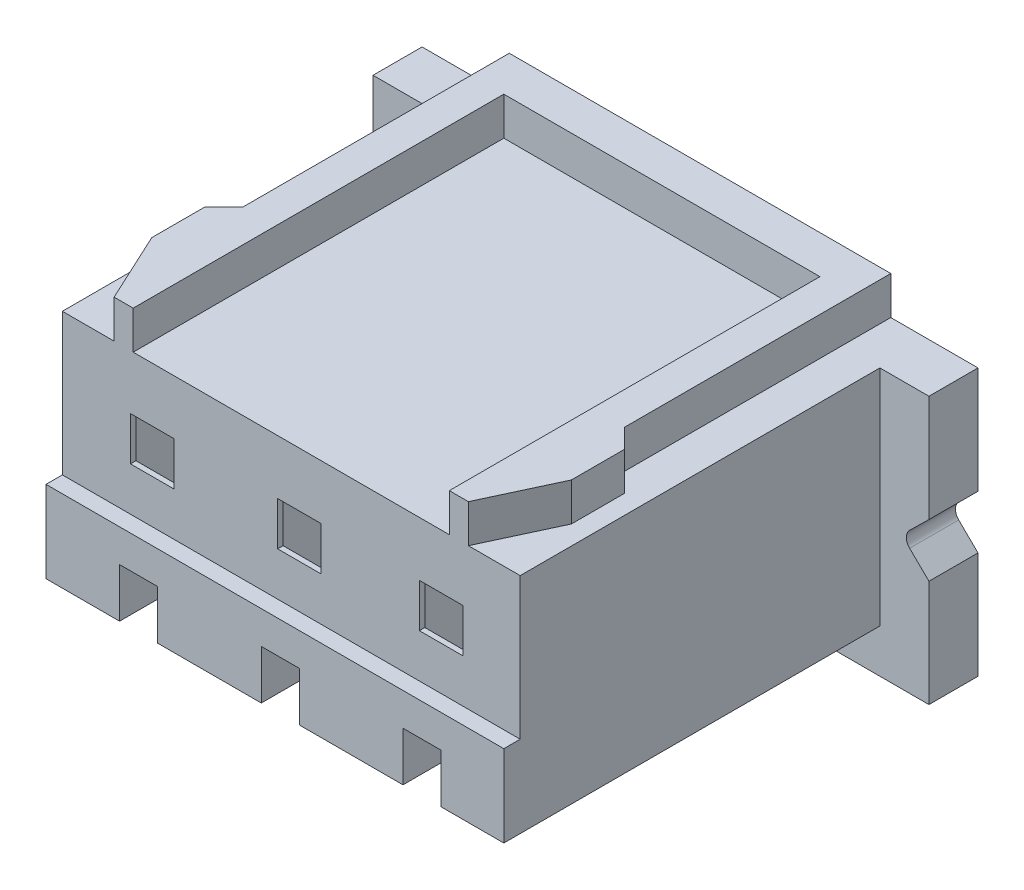
SolidWorks part; units mm, degrees
ref_plane "Plan de face" through (0, 0, 0) normal (0, 0, 1) x (1, 0, 0)
ref_plane "Plan de dessus" through (0, 0, 0) normal (0, 1, 0) x (1, 0, 0)
ref_plane "Plan de droite" through (0, 0, 0) normal (1, 0, 0) x (0, 0, -1)
sketch "Esquisse1" plane through (0, 0, 0) normal (0, 0, 1) x (1, 0, 0)
  line L1 (-5.1, 2.8) -> (5.1, 2.8)
  line L2 (-5.1, 2.8) -> (-5.1, -2.8)
  line L3 (-5.1, -2.8) -> (5.1, -2.8)
  line L4 (5.1, 2.8) -> (5.1, -2.8)
  line L5 (-5.1, 2.8) -> (5.1, -2.8) construction
  line L6 (-5.1, -2.8) -> (5.1, 2.8) construction
  point P0 (0, 0)
  dimension "D1" = 10.2
  dimension "D2" = 5.6
extrude "Boss.-Extru.1" add sketch "Esquisse1" against normal blind 7.8
sketch "Esquisse2" plane through (0, 0, 0) normal (0, 0, 1) x (1, 0, 0)
  line L0 (5.1, -2.8) -> (5.1, 2.8) construction
  line L1 (-5.1, 2.8) -> (5.1, 2.8)
  line L2 (-5.1, 2.8) -> (-5.1, -0.5)
  line L3 (-5.1, -0.5) -> (5.1, -0.5)
  line L4 (5.1, 2.8) -> (5.1, -0.5)
  dimension "D1" = 3.3
extrude "Enlèv. mat.-Extru.1" cut sketch "Esquisse2" against normal blind 0.3
sketch "Esquisse4" plane through (0, 0, 0) normal (0, 0, 1) x (1, 0, 0)
  line L0 (5.1, 2.8) -> (-5.1, 2.8) construction
  line L1 (-5.1, -2.8) -> (5.1, -2.8) construction
  line L2 (5.1, 2.8) -> (-5.1, 2.8)
  line L3 (-5.1, -2.8) -> (5.1, -2.8)
  line L4 (-4.2, 2.8) -> (-4.2, -2)
  line L5 (-4.2, -2) -> (4.2, -2)
  line L6 (4.2, -2) -> (4.2, 2.8)
  line L7 (-5.1, 2.8) -> (-5.1, -0.5) construction
  line L8 (5.1, -0.5) -> (5.1, 2.8) construction
  line L9 (-5.1, -0.5) -> (-5.1, -2.8) construction
  line L10 (5.1, -2.8) -> (5.1, -0.5) construction
  line L11 (-5.1, 2.8) -> (-5.1, -0.5)
  line L12 (-5.1, -0.5) -> (-5.1, -2.8)
  line L13 (5.1, -2.8) -> (5.1, -0.5)
  line L14 (5.1, -0.5) -> (5.1, 2.8)
  line M1 (5.1, -0.5) -> (-5.1, -0.5)
  line M2 (-5.1, -0.5) -> (-5.1, -2.8)
  line M3 (-5.1, -2.8) -> (5.1, -2.8)
  line M4 (5.1, -2.8) -> (5.1, -0.5)
  dimension "D1" = 0.9
  dimension "D2" = 0.9
  dimension "D3" = 0.8
extrude "Enlèv. mat.-Extru.2" cut sketch "Esquisse4" against normal blind 6.9 contours L2 L11 L4 M1 | L6 L5 L4 M1 M2 M3 M4 | L14 L2 L6 M1
sketch "Esquisse5" plane through (0, 2.8, 0) normal (0, 1, 0) x (1, 0, 0)
  line L0 (-3.5, 7.8) -> (-3.5, 2.91)
  line L1 (-3.5, 2.91) -> (-3.85, 2.56)
  line L2 (-3.85, 2.56) -> (-3.85, 1.59)
  line L3 (-3.85, 1.59) -> (-3.25, 0.3)
  line L4 (4.2, 0.3) -> (-4.2, 0.3) construction
  line L5 (-2.9, 0.3) -> (-2.9, 7.1)
  line L6 (-2.9, 7.1) -> (2.9, 7.1)
  line L7 (0, 7.8) -> (0, 0.3) construction
  line L8 (-5.1, 6.9) -> (-4.2, 6.9)
  line L9 (-4.2, 6.9) -> (-4.2, 0.3)
  line L10 (-4.2, 0.3) -> (4.2, 0.3)
  line L11 (4.2, 0.3) -> (4.2, 6.9)
  line L12 (4.2, 6.9) -> (5.1, 6.9)
  line L13 (5.1, 6.9) -> (5.1, 7.8)
  line L14 (5.1, 7.8) -> (-5.1, 7.8)
  line L15 (-5.1, 7.8) -> (-5.1, 6.9)
  line L16 (-5.1, 6.9) -> (-4.2, 6.9)
  line L17 (-4.2, 6.9) -> (-4.2, 0.3)
  line L18 (-4.2, 0.3) -> (4.2, 0.3)
  line L19 (4.2, 0.3) -> (4.2, 6.9)
  line L20 (4.2, 6.9) -> (5.1, 6.9)
  line L21 (5.1, 6.9) -> (5.1, 7.8)
  line L22 (5.1, 7.8) -> (-5.1, 7.8)
  line L23 (-5.1, 7.8) -> (-5.1, 6.9)
  line L24 (5.1, 7.8) -> (5.1, 6.9)
  line L25 (4.2, 6.9) -> (4.2, 0.3)
  line L26 (5.1, 6.9) -> (4.2, 6.9)
  line L27 (2.9, 0.3) -> (2.9, 7.1)
  line L28 (3.85, 1.59) -> (3.25, 0.3)
  line L29 (3.85, 2.56) -> (3.85, 1.59)
  line L30 (3.5, 2.91) -> (3.85, 2.56)
  line L31 (3.5, 7.8) -> (3.5, 2.91)
  point P21 (0, 7.1)
  line M9 (-5.1, 6.9) -> (-4.2, 6.9)
  line M10 (-4.2, 6.9) -> (-4.2, 0.3)
  line M11 (-4.2, 0.3) -> (4.2, 0.3)
  line M12 (4.2, 0.3) -> (4.2, 6.9)
  line M13 (4.2, 6.9) -> (5.1, 6.9)
  line M14 (5.1, 6.9) -> (5.1, 7.8)
  line M15 (5.1, 7.8) -> (-5.1, 7.8)
  line M16 (-5.1, 7.8) -> (-5.1, 6.9)
  dimension "D2" = 0.35
  dimension "D3" = 0.7
  dimension "D4" = 1.29
  dimension "D5" = 0.6
  dimension "D6" = 0.35
  dimension "D7" = 0.97
  dimension "D8" = 0.6
  dimension "D9" = 0.7
  dimension "D1" = 0
extrude "Enlèv. mat.-Extru.3" cut sketch "Esquisse5" against normal blind 0.7 contours L7 L6 L5 M11 | L6 L7 L18 L27 | L31 L30 L29 L28 M15 M11 M12 M13 M14 | L3 L2 L1 L0 M15 M16 M9 M10 M11
sketch "Esquisse6" plane through (0, 0, 0) normal (0, 0, 1) x (1, 0, 0)
  line L0 (-2.95, -2) -> (-2.95, -1.1)
  line L1 (-4.2, -2) -> (4.2, -2) construction
  line L2 (-2.95, -1.1) -> (-2.25, -1.1)
  line L3 (-2.25, -1.1) -> (-2.25, -2)
  line L4 (-4.2, -0.5) -> (-4.2, -2) construction
  line L5 (-0.25, -2) -> (-0.25, -1.1)
  line L6 (-0.25, -1.1) -> (0.45, -1.1)
  line L7 (0.45, -1.1) -> (0.45, -2)
  line L9 (2.35, -2) -> (2.35, -1.1)
  line L10 (2.35, -1.1) -> (3.05, -1.1)
  line L11 (3.05, -1.1) -> (3.05, -2)
  line L13 (-2.95, -2) -> (-2.25, -2)
  line L14 (-0.25, -2) -> (0.45, -2)
  line L15 (2.35, -2) -> (3.05, -2)
  dimension "D1" = 1.25
  dimension "D2" = 0.9
  dimension "D3" = 0.7
  dimension "D4" = 2
  dimension "D5" = 1.9
  dimension "D6" = 0.7
  dimension "D7" = 0.7
extrude "Enlèv. mat.-Extru.4" cut sketch "Esquisse6" against normal blind 3
sketch "Esquisse7" plane through (0, 0, -0.3) normal (0, 0, 1) x (1, 0, 0)
  line L0 (-2.9, 2.1) -> (2.9, 2.1) construction
  line L1 (-2.95, 1.1) -> (-2.15, 1.1)
  line L2 (-2.95, 1.1) -> (-2.95, 0.3)
  line L3 (-2.95, 0.3) -> (-2.15, 0.3)
  line L4 (-2.15, 1.1) -> (-2.15, 0.3)
  line L5 (-0.25, 1.1) -> (0.55, 1.1)
  line L6 (-0.25, 1.1) -> (-0.25, 0.3)
  line L7 (-0.25, 0.3) -> (0.55, 0.3)
  line L8 (0.55, 1.1) -> (0.55, 0.3)
  line L9 (2.35, 1.1) -> (3.15, 1.1)
  line L10 (2.35, 1.1) -> (2.35, 0.3)
  line L11 (2.35, 0.3) -> (3.15, 0.3)
  line L12 (3.15, 1.1) -> (3.15, 0.3)
  line L13 (-2.95, -1.1) -> (-2.95, -2) construction
  line L14 (-0.25, -1.1) -> (-0.25, -2) construction
  line L15 (2.35, -1.1) -> (2.35, -2) construction
  dimension "D1" = 0.8
  dimension "D2" = 1
extrude "Enlèv. mat.-Extru.5" cut sketch "Esquisse7" against normal blind 0.5
sketch "Esquisse8" plane through (0, 0, -7.8) normal (0, 0, -1) x (-1, 0, 0)
  line L0 (-0.8, 1.5) -> (-0.8, -1.5)
  line L1 (-0.8, 1.5) -> (0.8, 1.5)
  line L2 (0, 1.5) -> (0, 0) construction
  line L3 (-3.5, 2.8) -> (3.5, 2.8) construction
  line L4 (-0.8, -1.5) -> (-0.4, -1.5)
  line L5 (-0.4, -1.5) -> (-0.4, -1.7)
  line L6 (-0.4, -1.7) -> (0.4, -1.7)
  line L7 (0.4, -1.7) -> (0.4, -1.5)
  line L8 (0.4, -1.5) -> (0.8, -1.5)
  line L9 (0.8, -1.5) -> (0.8, 1.5)
  line L10 (0, 0) -> (0, -1.7) construction
  line L11 (-0.7, 0.95) -> (-0.7, -1.45)
  line L12 (-0.7, -1.45) -> (0.7, -1.45)
  line L13 (0.7, -1.45) -> (0.7, 0.95)
  line L14 (0, -1.45) -> (0, 0.95) construction
  line L15 (1.7, 1.5) -> (1.7, -1.5)
  line L16 (1.7, 1.5) -> (3.3, 1.5)
  line L17 (1.7, -1.5) -> (2.1, -1.5)
  line L18 (2.1, -1.5) -> (2.1, -1.7)
  line L19 (2.1, -1.7) -> (2.9, -1.7)
  line L20 (2.9, -1.7) -> (2.9, -1.5)
  line L21 (2.9, -1.5) -> (3.3, -1.5)
  line L22 (3.3, -1.5) -> (3.3, 1.5)
  line L23 (1.8, 0.95) -> (1.8, -1.45)
  line L24 (1.8, -1.45) -> (3.2, -1.45)
  line L25 (3.2, -1.45) -> (3.2, 0.95)
  line L26 (2.5, 1.5) -> (2.5, 0) construction
  line L27 (2.5, 0) -> (2.5, -1.7) construction
  line L28 (2.5, -1.45) -> (2.5, 0.95) construction
  line L29 (-3.3, 1.5) -> (-3.3, -1.5)
  line L30 (-3.3, 1.5) -> (-1.7, 1.5)
  line L31 (-3.3, -1.5) -> (-2.9, -1.5)
  line L32 (-2.9, -1.5) -> (-2.9, -1.7)
  line L33 (-2.9, -1.7) -> (-2.1, -1.7)
  line L34 (-2.1, -1.7) -> (-2.1, -1.5)
  line L35 (-2.1, -1.5) -> (-1.7, -1.5)
  line L36 (-1.7, -1.5) -> (-1.7, 1.5)
  line L37 (-3.2, 0.95) -> (-3.2, -1.45)
  line L38 (-3.2, -1.45) -> (-1.8, -1.45)
  line L39 (-1.8, -1.45) -> (-1.8, 0.95)
  line L40 (-2.5, 1.5) -> (-2.5, 0) construction
  line L41 (-2.5, 0) -> (-2.5, -1.7) construction
  line L42 (-2.5, -1.45) -> (-2.5, 0.95) construction
  arc A0 (-0.7, 0.95) -> (0, 0.95) centre (-0.35, 0.95) cw
  arc A1 (0, 0.95) -> (0.7, 0.95) centre (0.35, 0.95) cw
  arc A2 (1.8, 0.95) -> (2.5, 0.95) centre (2.15, 0.95) cw
  arc A3 (2.5, 0.95) -> (3.2, 0.95) centre (2.85, 0.95) cw
  arc A4 (-3.2, 0.95) -> (-2.5, 0.95) centre (-2.85, 0.95) cw
  arc A5 (-2.5, 0.95) -> (-1.8, 0.95) centre (-2.15, 0.95) cw
  dimension "D1" = 3
  dimension "D2" = 1.6
  dimension "D3" = 1.3
  dimension "D4" = 0.8
  dimension "D5" = 0.2
  dimension "D6" = 0.05
  dimension "D7" = 0.1
  dimension "D8" = 0.1
  dimension "D9" = 2.4
  dimension "D11" = 2.5
  dimension "D13" = 2.5
  dimension "D10" = 2
  dimension "D12" = 2
extrude "Enlèv. mat.-Extru.6" cut sketch "Esquisse8" against normal blind 7 contours L8 L9 L1 L0 L4 L5 L6 L7 A0 A1 L13 L12 L11 | L35 L36 L30 L29 L31 L32 L33 L34 A4 A5 L39 L38 L37 | L21 L22 L16 L15 L17 L18 L19 L20 A2 A3 L25 L24 L23
sketch "Esquisse9" plane through (0, 0, -7.8) normal (0, 0, -1) x (-1, 0, 0)
  line L0 (-0.7, 0.95) -> (-0.7, -1.45) construction
  line L1 (-0.7, -1.45) -> (0.7, -1.45) construction
  line L2 (0.7, -1.45) -> (0.7, 0.95) construction
  line L3 (-3.2, 0.95) -> (-3.2, -1.45) construction
  line L4 (-3.2, -1.45) -> (-1.8, -1.45) construction
  line L5 (-1.8, -1.45) -> (-1.8, 0.95) construction
  line L6 (1.8, 0.95) -> (1.8, -1.45) construction
  line L7 (1.8, -1.45) -> (3.2, -1.45) construction
  line L8 (3.2, -1.45) -> (3.2, 0.95) construction
  line L9 (-0.7, 0.95) -> (-0.7, -1.45)
  line L10 (-0.7, -1.45) -> (0.7, -1.45)
  line L11 (0.7, -1.45) -> (0.7, 0.95)
  line L12 (-3.2, 0.95) -> (-3.2, -1.45)
  line L13 (-3.2, -1.45) -> (-1.8, -1.45)
  line L14 (-1.8, -1.45) -> (-1.8, 0.95)
  line L15 (1.8, 0.95) -> (1.8, -1.45)
  line L16 (1.8, -1.45) -> (3.2, -1.45)
  line L17 (3.2, -1.45) -> (3.2, 0.95)
  arc A0 (0.7, 0.95) -> (0, 0.95) centre (0.35, 0.95) ccw construction
  arc A1 (0, 0.95) -> (-0.7, 0.95) centre (-0.35, 0.95) ccw construction
  arc A2 (-1.8, 0.95) -> (-2.5, 0.95) centre (-2.15, 0.95) ccw construction
  arc A3 (-2.5, 0.95) -> (-3.2, 0.95) centre (-2.85, 0.95) ccw construction
  arc A4 (3.2, 0.95) -> (2.5, 0.95) centre (2.85, 0.95) ccw construction
  arc A5 (2.5, 0.95) -> (1.8, 0.95) centre (2.15, 0.95) ccw construction
  arc A6 (0.7, 0.95) -> (0, 0.95) centre (0.35, 0.95) ccw
  arc A7 (0, 0.95) -> (-0.7, 0.95) centre (-0.35, 0.95) ccw
  arc A8 (-1.8, 0.95) -> (-2.5, 0.95) centre (-2.15, 0.95) ccw
  arc A9 (-2.5, 0.95) -> (-3.2, 0.95) centre (-2.85, 0.95) ccw
  arc A10 (3.2, 0.95) -> (2.5, 0.95) centre (2.85, 0.95) ccw
  arc A11 (2.5, 0.95) -> (1.8, 0.95) centre (2.15, 0.95) ccw
extrude "Enlèv. mat.-Extru.7" cut sketch "Esquisse9" against normal blind 0.8
sketch "Esquisse10" plane through (0, 0, -7) normal (0, 0, -1) x (-1, 0, 0)
  line L0 (0, -1.45) -> (0, 0) construction
  line L1 (-0.7, -1.45) -> (0.7, -1.45) construction
  line L2 (-2.5, 0) -> (0, 0) construction
  line L3 (0, 0) -> (2.5, 0) construction
  line L4 (-2.5, 0) -> (-2.5, -1.45) construction
  line L5 (-3.2, -1.45) -> (-1.8, -1.45) construction
  line L6 (2.5, 0) -> (2.5, -1.45) construction
  line L7 (1.8, -1.45) -> (3.2, -1.45) construction
  circle A0 centre (0, 0) radius 0.6
  circle A1 centre (-2.5, 0) radius 0.6
  circle A2 centre (2.5, 0) radius 0.6
  dimension "D2" = 1.2
  dimension "D1" = 1.45
extrude "Enlèv. mat.-Extru.8" cut sketch "Esquisse10" against normal blind 4
ref_plane "Plan1" through (0, -1.9735, 0.2288) normal (0, -0.9933, 0.1152) x (-1, 0, 0)
sketch "Sketch2" plane through (0, 0, -7.8) normal (0, 0, -1) x (-1, 0, 0)
  line L8 (3.3, -1.5) -> (3.3, 1.5)
  line L9 (3.3, -1.5) -> (3.3, 1.5)
  line L10 (2.9, -1.5) -> (3.3, -1.5)
  line L11 (2.9, -1.5) -> (3.3, -1.5)
  line L12 (2.9, -1.7) -> (2.9, -1.5)
  line L13 (2.9, -1.7) -> (2.9, -1.5)
  line L14 (2.1, -1.7) -> (2.9, -1.7)
  line L15 (2.1, -1.7) -> (2.9, -1.7)
  line L16 (2.1, -1.5) -> (2.1, -1.7)
  line L17 (2.1, -1.5) -> (2.1, -1.7)
  line L18 (1.7, -1.5) -> (2.1, -1.5)
  line L19 (1.7, -1.5) -> (2.1, -1.5)
  line L20 (1.7, 1.5) -> (1.7, -1.5)
  line L21 (1.7, 1.5) -> (1.7, -1.5)
  line L22 (3.3, 1.5) -> (1.7, 1.5)
  line L23 (3.3, 1.5) -> (1.7, 1.5)
  line L32 (0.8, -1.5) -> (0.8, 1.5)
  line L33 (0.4, -1.5) -> (0.8, -1.5)
  line L34 (0.4, -1.7) -> (0.4, -1.5)
  line L35 (-0.4, -1.7) -> (0.4, -1.7)
  line L36 (-0.4, -1.5) -> (-0.4, -1.7)
  line L37 (-0.8, -1.5) -> (-0.4, -1.5)
  line L38 (-0.8, 1.5) -> (-0.8, -1.5)
  line L39 (0.8, 1.5) -> (-0.8, 1.5)
  line L48 (-1.7, -1.5) -> (-1.7, 1.5)
  line L49 (-2.1, -1.5) -> (-1.7, -1.5)
  line L50 (-2.1, -1.7) -> (-2.1, -1.5)
  line L51 (-2.9, -1.7) -> (-2.1, -1.7)
  line L52 (-2.9, -1.5) -> (-2.9, -1.7)
  line L53 (-3.3, -1.5) -> (-2.9, -1.5)
  line L54 (-3.3, 1.5) -> (-3.3, -1.5)
  line L55 (-1.7, 1.5) -> (-3.3, 1.5)
  dimension "D1" = 0
sketch "Sketch3" plane through (0, 0, -7.8) normal (0, 0, -1) x (-1, 0, 0)
  line L0 (3.6, 1.5) -> (-3.938, 1.5) construction
  line L1 (1, 1.5) -> (1, -1.3)
  line L2 (-1.2, -1.3) -> (-1.2, 1.5)
  line L3 (-0.45, -1.3) -> (-1.2, -1.3)
  line L4 (2.85, -1.7) -> (2.85, -1.3)
  line L5 (2.85, -1.7) -> (2.15, -1.7)
  line L6 (-0.45, -1.7) -> (-0.45, -1.3)
  line L7 (0.25, -1.7) -> (0.25, -1.3)
  line L8 (2.5, -1.7) -> (2.5, 1.5) construction
  line L9 (2.1, -1.7) -> (2.9, -1.7) construction
  line L10 (3.6, 1.5) -> (1.4, 1.5)
  line L11 (1, -1.3) -> (0.25, -1.3)
  line L12 (0.25, -1.7) -> (-0.45, -1.7)
  line L13 (1, 1.5) -> (-1.2, 1.5)
  line L14 (-0.8, 1.5) -> (0.8, 1.5) construction
  line L15 (-1.6, 1.5) -> (-1.6, -1.3)
  line L16 (-3.8, -1.3) -> (-3.8, 1.5)
  line L17 (-3.05, -1.3) -> (-3.8, -1.3)
  line L18 (-3.05, -1.7) -> (-3.05, -1.3)
  line L19 (-2.35, -1.7) -> (-2.35, -1.3)
  line L20 (-1.6, -1.3) -> (-2.35, -1.3)
  line L21 (-2.35, -1.7) -> (-3.05, -1.7)
  line L22 (-1.6, 1.5) -> (-3.8, 1.5)
  line L23 (-0.4, -1.7) -> (0.4, -1.7) construction
  line L26 (1.7, 1.5) -> (3.3, 1.5) construction
  line L27 (2.15, -1.7) -> (2.15, -1.3)
  line L28 (2.15, -1.3) -> (1.4, -1.3)
  line L29 (1.4, -1.3) -> (1.4, 1.5)
  line L30 (3.6, 1.5) -> (3.6, -1.3)
  line L31 (3.6, -1.3) -> (2.85, -1.3)
  dimension "D1" = 0.7
  dimension "D2" = 2.2
  dimension "D3" = 2.8
  dimension "D4" = 0.4
  dimension "D6" = 0.4
  dimension "D5" = 3
extrude "Cut-Extrude2" cut sketch "Sketch3" against normal blind 7.4
sketch "Sketch4" plane through (0, 0, -7.8) normal (0, 0, -1) x (-1, 0, 0)
  line L0 (2.85, -1.7) -> (2.85, -1.3) construction
  line L1 (2.85, -1.7) -> (2.15, -1.7) construction
  line L2 (2.15, -1.7) -> (2.15, -1.3) construction
  line L3 (2.15, -1.3) -> (1.4, -1.3) construction
  line L4 (1.4, -1.3) -> (1.4, 1.5) construction
  line L5 (3.6, 1.5) -> (1.4, 1.5) construction
  line L6 (3.6, 1.5) -> (3.6, -1.3) construction
  line L7 (3.6, -1.3) -> (2.85, -1.3) construction
  line L8 (0.25, -1.7) -> (0.25, -1.3) construction
  line L9 (0.25, -1.7) -> (-0.45, -1.7) construction
  line L10 (-0.45, -1.7) -> (-0.45, -1.3) construction
  line L11 (-0.45, -1.3) -> (-1.2, -1.3) construction
  line L12 (-1.2, -1.3) -> (-1.2, 1.5) construction
  line L13 (1, 1.5) -> (-1.2, 1.5) construction
  line L14 (1, 1.5) -> (1, -1.3) construction
  line L15 (1, -1.3) -> (0.25, -1.3) construction
  line L16 (-1.6, -1.3) -> (-2.35, -1.3) construction
  line L17 (-1.6, 1.5) -> (-1.6, -1.3) construction
  line L18 (-1.6, 1.5) -> (-3.8, 1.5) construction
  line L19 (-3.8, -1.3) -> (-3.8, 1.5) construction
  line L20 (-3.05, -1.3) -> (-3.8, -1.3) construction
  line L21 (-3.05, -1.7) -> (-3.05, -1.3) construction
  line L22 (-2.35, -1.7) -> (-3.05, -1.7) construction
  line L23 (-2.35, -1.7) -> (-2.35, -1.3) construction
  line L24 (2.85, -1.7) -> (2.85, -1.3)
  line L25 (2.85, -1.7) -> (2.15, -1.7)
  line L26 (2.15, -1.7) -> (2.15, -1.3)
  line L27 (2.15, -1.3) -> (1.4, -1.3)
  line L28 (1.4, -1.3) -> (1.4, 1.5)
  line L29 (3.6, 1.5) -> (1.4, 1.5)
  line L30 (3.6, 1.5) -> (3.6, -1.3)
  line L31 (3.6, -1.3) -> (2.85, -1.3)
  line L32 (0.25, -1.7) -> (0.25, -1.3)
  line L33 (0.25, -1.7) -> (-0.45, -1.7)
  line L34 (-0.45, -1.7) -> (-0.45, -1.3)
  line L35 (-0.45, -1.3) -> (-1.2, -1.3)
  line L36 (-1.2, -1.3) -> (-1.2, 1.5)
  line L37 (1, 1.5) -> (-1.2, 1.5)
  line L38 (1, 1.5) -> (1, -1.3)
  line L39 (1, -1.3) -> (0.25, -1.3)
  line L40 (-1.6, -1.3) -> (-2.35, -1.3)
  line L41 (-1.6, 1.5) -> (-1.6, -1.3)
  line L42 (-1.6, 1.5) -> (-3.8, 1.5)
  line L43 (-3.8, -1.3) -> (-3.8, 1.5)
  line L44 (-3.05, -1.3) -> (-3.8, -1.3)
  line L45 (-3.05, -1.7) -> (-3.05, -1.3)
  line L46 (-2.35, -1.7) -> (-3.05, -1.7)
  line L47 (-2.35, -1.7) -> (-2.35, -1.3)
  line L48 (3.3, -1.3) -> (3.3, -1.7)
  line L49 (3.3, -1.7) -> (2.85, -1.7)
  line L50 (2.15, -1.7) -> (1.7, -1.7)
  line L51 (1.7, -1.7) -> (1.7, -1.3)
  line L52 (0.8, -1.3) -> (0.8, -1.7)
  line L53 (0.8, -1.7) -> (0.25, -1.7)
  line L54 (0.25, -1.7) -> (0.2517, -1.6946)
  line L55 (-0.8, -1.3) -> (-0.8, -1.7)
  line L56 (-0.8, -1.7) -> (-0.45, -1.7)
  line L57 (-1.7, -1.3) -> (-1.7, -1.7)
  line L58 (-1.7, -1.7) -> (-2.35, -1.7)
  line L59 (-2.35, -1.7) -> (-2.3485, -1.7022)
  line L60 (-3.3, -1.3) -> (-3.3, -1.7)
  line L61 (-3.3, -1.7) -> (-3.05, -1.7)
extrude "Boss-Extrude2" add sketch "Sketch4" against normal blind 7
sketch "Sketch5" plane through (0, -2, 0) normal (0, -1, 0) x (1, 0, 0)
  line L1 (-2.95, -0.4) -> (-2.25, -0.4)
  line L2 (-2.95, -0.4) -> (-2.95, -3)
  line L3 (-2.95, -3) -> (-2.25, -3)
  line L4 (-2.25, -0.4) -> (-2.25, -3)
  line L5 (-0.25, -0.4081) -> (0.45, -0.4081)
  line L6 (-0.25, -0.4081) -> (-0.25, -3)
  line L7 (-0.25, -3) -> (0.45, -3)
  line L8 (0.45, -0.4081) -> (0.45, -3)
  line L9 (2.35, -0.4) -> (3.05, -0.4)
  line L10 (2.35, -0.4) -> (2.35, -3)
  line L11 (2.35, -3) -> (3.05, -3)
  line L12 (3.05, -0.4) -> (3.05, -3)
  line L16 (3.05, -3) -> (3.05, 0) construction
  line L22 (-2.25, -3) -> (-2.25, 0) construction
  line L23 (0.45, -3) -> (0.45, 0) construction
extrude "Cut-Extrude3" cut sketch "Sketch5" against normal blind 2
sketch "Sketch7" plane through (0, 0, -7.8) normal (0, 0, -1) x (-1, 0, 0)
  line L0 (-5.1, 0.1399) -> (-4.6, -0.35)
  line L1 (-5.1, -2.8) -> (-5.1, 2.1) construction
  line L2 (-4.6, -0.35) -> (-5.1, -0.8399)
  line L4 (-5.1, 0.1399) -> (-5.1, -0.8399)
  point P8 (-5.6192, -0.35)
  dimension "D1" = 0.5
  dimension "D2" = 0.7
  dimension "D3" = 0.7
extrude "Cut-Extrude4" cut sketch "Sketch7" against normal blind 10
fillet "Fillet1" radius 0.2 1 edges at (4.6, -0.35, -7.35)
sketch "Sketch8" plane through (0, 0, -3) normal (0, 0, 1) x (1, 0, 0)
  line L0 (-2.95, -2) -> (-2.25, -2) construction
  line L1 (-2.95, -1.3) -> (-2.85, -1.3)
  line L2 (-2.95, -1.3) -> (-2.95, -2)
  line L3 (-2.95, -2) -> (-2.85, -2)
  line L4 (-2.85, -1.3) -> (-2.85, -2)
  line L5 (-2.85, -1.3) -> (-2.85, -1.7) construction
extrude "Boss-Extrude3" add sketch "Sketch8" along normal up to surface (3 mm away) contours L4 L3 L2 L1 up to face at (0.05, -1.475, 0)
sketch "Sketch9" plane through (-2.95, 0, 0) normal (1, 0, 0) x (0, 0, -1)
  line L1 (0, -1.1) -> (0.4, -1.1)
  line L2 (0, -1.1) -> (0, -1.3)
  line L3 (0, -1.3) -> (0.4, -1.3)
  line L4 (0.4, -1.1) -> (0.4, -1.3)
extrude "Boss-Extrude4" add sketch "Sketch9" along normal up to surface (0.1 mm away) up to face at (-2.85, -1.6667, -3.6)
sketch "Sketch12" plane through (0, -1.7, 0) normal (0, 1, 0) x (1, 0, 0)
  line L1 (-2.15, 0.4) -> (-2.25, 0.4)
  line L2 (-2.15, 0.4) -> (-2.15, 3)
  line L3 (-2.15, 3) -> (-2.25, 3)
  line L4 (-2.25, 0.4) -> (-2.25, 3)
extrude "Cut-Extrude5" cut sketch "Sketch12" against normal blind 10
sketch "Sketch13" plane through (0, 0, -0.4) normal (0, 0, -1) x (-1, 0, 0)
  line L0 (2.15, -2) -> (2.15, -1.3) construction
  line L1 (2.15, -2) -> (2.25, -2)
  line L2 (2.15, -2) -> (2.15, -1.1)
  line L3 (2.15, -1.1) -> (2.25, -1.1)
  line L4 (2.25, -2) -> (2.25, -1.1)
extrude "Cut-Extrude6" cut sketch "Sketch13" against normal blind 10 contours L4 L3 L2 L1
